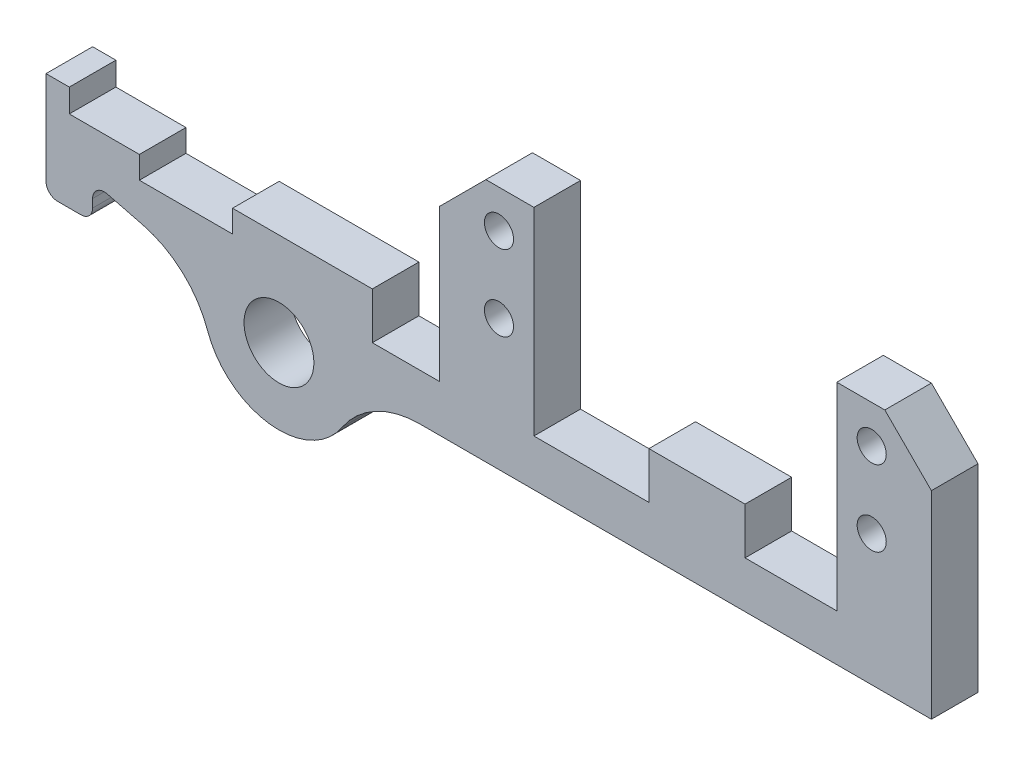
SolidWorks part; units mm, degrees
ref_plane "Front Plane" through (0, 0, 0) normal (0, 0, 1) x (1, 0, 0)
ref_plane "Top Plane" through (0, 0, 0) normal (0, 1, 0) x (1, 0, 0)
ref_plane "Right Plane" through (0, 0, 0) normal (1, 0, 0) x (0, 0, -1)
sketch "Sketch1" plane through (0, 136.6763, 0) normal (0, 1, 0) x (1, 0, 0)
  line L0 (-27.651, -32.4827) -> (-27.651, -60.4545) construction
  line L1 (-103.851, -54.1033) -> (-90.951, -54.1033)
  line L2 (-103.851, -54.1033) -> (-103.851, -60.4533)
  line L3 (-103.851, -60.4533) -> (-90.951, -60.4533)
  line L4 (-90.951, -54.1033) -> (-90.951, -60.4533)
  line L5 (-68.926, -54.1033) -> (-81.826, -54.1033)
  line L6 (-68.926, -54.1033) -> (-68.926, -60.4533)
  line L7 (-68.926, -60.4533) -> (-81.826, -60.4533)
  line L8 (-81.826, -54.1033) -> (-81.826, -60.4533)
  line L9 (-53.251, -54.1033) -> (-40.151, -54.1033)
  line L10 (-53.251, -54.1033) -> (-53.251, -60.4533)
  line L11 (-53.251, -60.4533) -> (-40.151, -60.4533)
  line L12 (-40.151, -54.1033) -> (-40.151, -60.4533)
  line L13 (-27.651, -54.1033) -> (-14.751, -54.1033)
  line L14 (-27.651, -54.1033) -> (-27.651, -60.4533)
  line L15 (-27.651, -60.4533) -> (-14.751, -60.4533)
  line L16 (-14.751, -54.1033) -> (-14.751, -60.4533)
  dimension "D1" = 12.9
  dimension "D2" = 13.1
  dimension "D3" = 12.9
  dimension "D4" = 12.9
  dimension "D5" = 50.6
extrude "Boss-Extrude1" add sketch "Sketch1" against normal blind 6.35
sketch "Sketch2" plane through (0, 130.3263, 0) normal (0, -1, 0) x (-1, 0, 0)
  line L1 (103.851, -60.4533) -> (14.951, -60.4533)
  line L2 (103.851, -60.4533) -> (103.851, -54.1033)
  line L3 (103.851, -54.1033) -> (14.951, -54.1033)
  line L4 (14.951, -60.4533) -> (14.951, -54.1033)
  dimension "D1" = 6.35
  dimension "D2" = 88.9
extrude "Boss-Extrude2" add sketch "Sketch2" along normal blind 12.7
sketch "Sketch3" plane through (0, 136.6763, 0) normal (0, 1, 0) x (1, 0, 0)
  line L1 (-68.926, -54.1033) -> (-81.826, -54.1033)
  line L2 (-68.926, -54.1033) -> (-68.926, -60.4533)
  line L3 (-68.926, -60.4533) -> (-81.826, -60.4533)
  line L4 (-81.826, -54.1033) -> (-81.826, -60.4533)
  line L5 (-14.751, -54.1033) -> (-27.651, -54.1033)
  line L6 (-14.751, -54.1033) -> (-14.751, -60.4533)
  line L7 (-14.751, -60.4533) -> (-27.651, -60.4533)
  line L8 (-27.651, -54.1033) -> (-27.651, -60.4533)
extrude "Boss-Extrude3" add sketch "Sketch3" along normal up to surface (20.6375 mm away)
chamfer "Chamfer1" distance 6.35 angle 45 2 edges at (-14.751, 157.3138, 57.2783) (-81.826, 157.3138, 57.2783)
sketch "Sketch4" plane through (0, 0, 60.4533) normal (0, 0, 1) x (1, 0, 0)
  circle A0 centre (-73.6885, 152.1544) radius 1.9844
  circle A1 centre (-73.6885, 141.8357) radius 1.9844
  circle A2 centre (-22.8885, 141.8357) radius 1.9844
  circle A3 centre (-22.8885, 152.1544) radius 1.9844
extrude "Cut-Extrude1" cut sketch "Sketch4" against normal through all
sketch "Sketch12" plane through (-14.951, 0, 0) normal (1, 0, 0) x (0, 0, -1)
  line L1 (-60.4533, 117.6263) -> (-54.1033, 117.6263)
  line L2 (-60.4533, 117.6263) -> (-60.4533, 130.3263)
  line L3 (-60.4533, 130.3263) -> (-54.1033, 130.3263)
  line L4 (-54.1033, 117.6263) -> (-54.1033, 130.3263)
extrude "Boss-Extrude6" add sketch "Sketch12" along normal up to surface (0.2 mm away) up to face at (-14.751, 140.645, 57.2783)
sketch "Sketch13" plane through (0, 0, 60.4533) normal (0, 0, 1) x (1, 0, 0)
  line L0 (-14.751, 117.6263) -> (-14.751, 150.9638) construction
  line L1 (-103.851, 117.6263) -> (-14.751, 117.6263)
  line L2 (-103.851, 117.6263) -> (-103.851, 123.9763)
  line L3 (-103.851, 123.9763) -> (-14.751, 123.9763)
  line L4 (-14.751, 117.6263) -> (-14.751, 123.9763)
  dimension "D1" = 6.35
extrude "Cut-Extrude2" cut sketch "Sketch13" against normal through all
sketch "Sketch14" plane through (0, 0, 60.4533) normal (0, 0, 1) x (1, 0, 0)
  line L1 (-132.251, 139.8513) -> (-135.426, 139.8513)
  line L2 (-132.251, 139.8513) -> (-132.251, 136.6763)
  line L4 (-135.426, 139.8513) -> (-135.426, 131.9138)
  line L5 (-103.851, 123.9763) -> (-135.426, 131.9138)
  line L6 (-103.851, 136.6763) -> (-132.251, 136.6763)
  line L7 (-103.851, 136.6763) -> (-103.851, 123.9763)
  dimension "D2" = 3.175
  dimension "D3" = 28.4
extrude "Boss-Extrude7" add sketch "Sketch14" against normal blind 6.35
sketch "Sketch19" plane through (0, 0, 60.4533) normal (0, 0, 1) x (1, 0, 0)
  circle A0 centre (-103.676, 123.9763) radius 10.3188
  circle A1 centre (-103.676, 123.9763) radius 4.7625
extrude "Boss-Extrude8" add sketch "Sketch19" against normal blind 6.35
sketch "Sketch20" plane through (0, 0, 60.4533) normal (0, 0, 1) x (1, 0, 0)
  circle A0 centre (-103.676, 123.9763) radius 4.7625
extrude "Cut-Extrude3" cut sketch "Sketch20" against normal through all both and the other way through all
fillet "Fillet2" radius 12.7 2 edges at (-113.6937, 126.4506, 57.2783) (-93.3572, 123.9763, 57.2783)
sketch "Sketch21" plane through (0, 0, 60.4533) normal (0, 0, 1) x (1, 0, 0)
  line L1 (-135.426, 131.9138) -> (-129.076, 131.9138)
  line L2 (-135.426, 131.9138) -> (-135.426, 125.5638)
  line L3 (-135.426, 125.5638) -> (-129.076, 125.5638)
  line L4 (-129.076, 131.9138) -> (-129.076, 125.5638)
  dimension "D1" = 6.35
  dimension "D2" = 6.35
extrude "Boss-Extrude9" add sketch "Sketch21" against normal up to surface (6.35 mm away) up to face at (-98.9135, 123.9763, 54.1033)
fillet "Fillet4" radius 1.5875 3 edges at (-129.076, 130.3175, 57.2783) (-135.426, 125.5638, 57.2783) (-129.076, 125.5638, 57.2783)
sketch "Sketch22" plane through (0, 0, 60.4533) normal (0, 0, 1) x (1, 0, 0)
  line L0 (-132.251, 136.6763) -> (-90.951, 136.6763) construction
  line L1 (-122.701, 136.6763) -> (-110.001, 136.6763)
  line L2 (-122.701, 136.6763) -> (-122.701, 133.6283)
  line L3 (-122.701, 133.6283) -> (-110.001, 133.6283)
  line L4 (-110.001, 136.6763) -> (-110.001, 133.6283)
  line L5 (-90.951, 130.3263) -> (-90.951, 136.6763) construction
  dimension "D1" = 3.048
  dimension "D2" = 12.7
  dimension "D3" = 19.05
extrude "Cut-Extrude4" cut sketch "Sketch22" against normal through all
